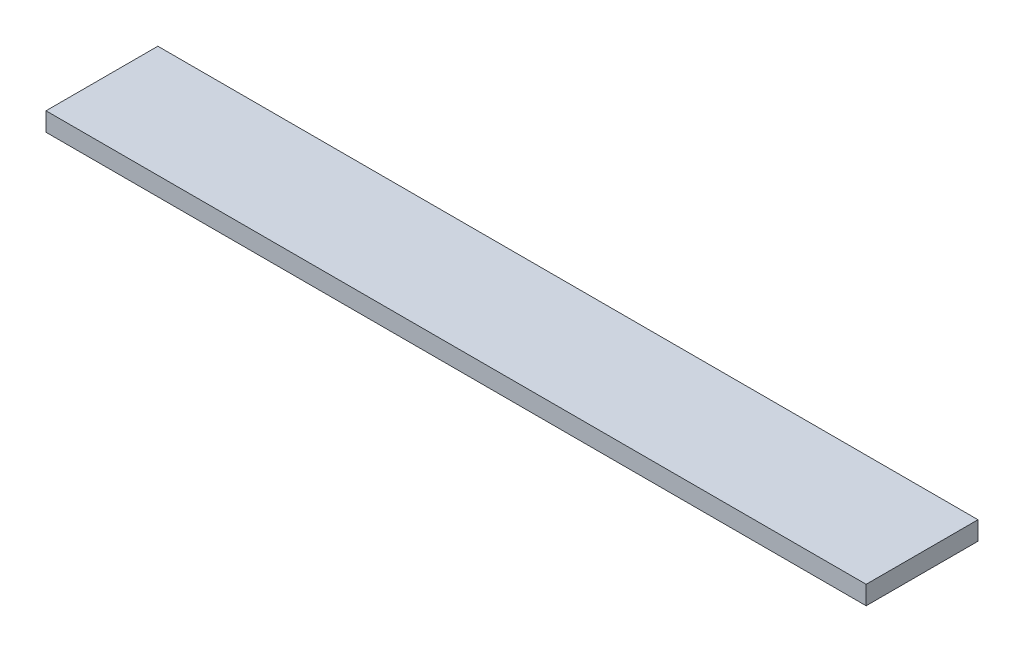
SolidWorks part; units mm, degrees
ref_plane "Front Plane" through (0, 0, 0) normal (0, 0, 1) x (1, 0, 0)
ref_plane "Top Plane" through (0, 0, 0) normal (0, 1, 0) x (1, 0, 0)
ref_plane "Right Plane" through (0, 0, 0) normal (1, 0, 0) x (0, 0, -1)
sketch "Sketch1" plane through (0, 0, 0) normal (0, 1, 0) x (1, 0, 0)
  line L1 (-87.5655, 41.0362) -> (471.2345, 41.0362)
  line L2 (-87.5655, 41.0362) -> (-87.5655, -35.1638)
  line L3 (-87.5655, -35.1638) -> (471.2345, -35.1638)
  line L4 (471.2345, 41.0362) -> (471.2345, -35.1638)
  dimension "D1" = 558.8
  dimension "D2" = 76.2
extrude "Boss-Extrude1" add sketch "Sketch1" along normal blind 12.7
